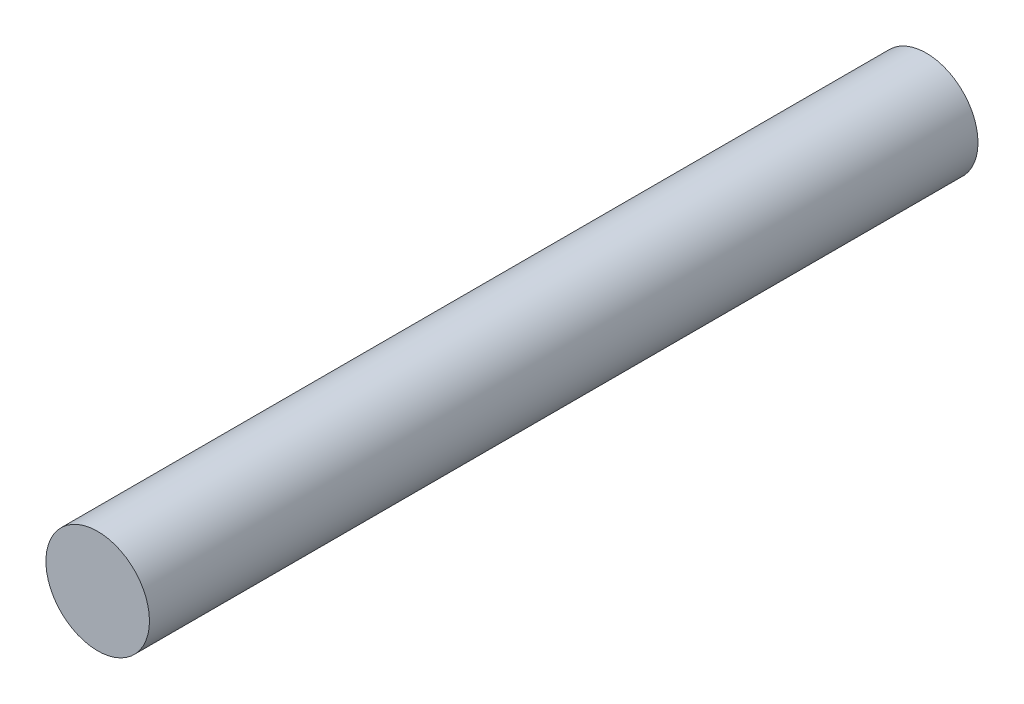
SolidWorks part; units mm, degrees
ref_plane "Ön Düzlem" through (0, 0, 0) normal (0, 0, 1) x (1, 0, 0)
ref_plane "Üst Düzlem" through (0, 0, 0) normal (0, 1, 0) x (1, 0, 0)
ref_plane "Sağ Düzlem" through (0, 0, 0) normal (1, 0, 0) x (0, 0, -1)
sketch "Çizim1" plane through (0, 0, 0) normal (0, 0, 1) x (1, 0, 0)
  circle A0 centre (0, 0) radius 2.5
  dimension "D1" = 5
extrude "Yükseklik-Ekstrüzyon1" add sketch "Çizim1" along normal blind 40
